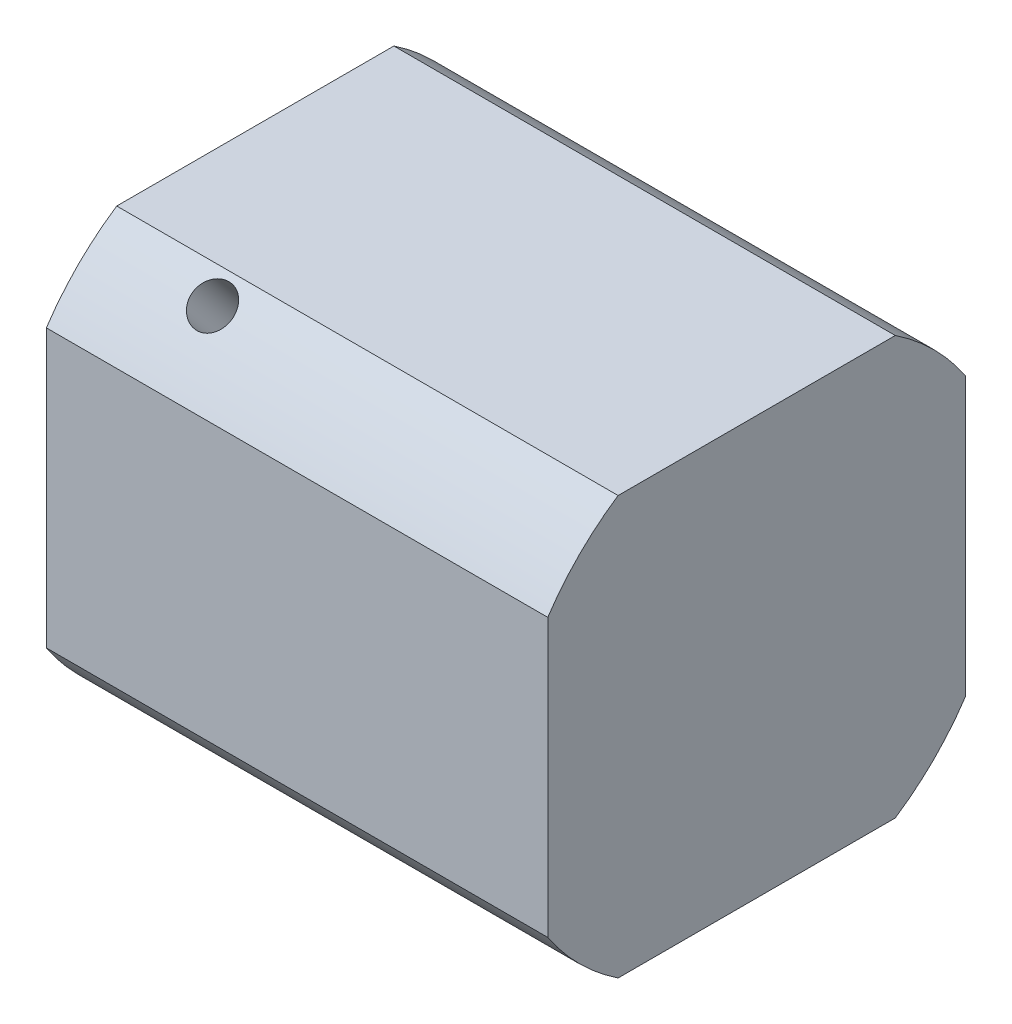
SolidWorks part; units mm, degrees
ref_plane "Front Plane" through (0, 0, 0) normal (0, 0, 1) x (1, 0, 0)
ref_plane "Top Plane" through (0, 0, 0) normal (0, 1, 0) x (1, 0, 0)
ref_plane "Right Plane" through (0, 0, 0) normal (1, 0, 0) x (0, 0, -1)
sketch "Sketch1" plane through (0, 0, 0) normal (0, 1, 0) x (1, 0, 0)
  line L0 (0, 0) -> (0, 19.05)
  line L1 (0, 19.05) -> (38.1, 19.05)
  line L2 (38.1, 19.05) -> (38.1, 9.525)
  line L5 (0, 0) -> (38.1, 0)
  line L6 (38.1, 9.525) -> (38.1, 0)
  dimension "D1" = 19.05
  dimension "D2" = 38.1
  dimension "D4" = 9.525
revolve "Revolve1" add sketch "Sketch1" angle 360 about L5
hole_wizard "Tap Drill for M3 Helicoil1" positions "3DSketch4" profile "Sketch8" hole size "M3x0.5" standard "ANSI Metric" end condition through all
sketch3d "3DSketch4"
  point P0 (8.9414, 14.6267, 12.205)
sketch "Sketch8" plane through (8.9414, 14.6267, 12.205) normal (1, 0, 0) x (0, -0.6407, 0.7678)
  line L0 (0, 0) -> (0, 45.8817)
  line L1 (0, 45.8817) -> (1.575, 45.8817)
  line L2 (1.575, 45.8817) -> (1.575, 0)
  line L5 (1.575, 0) -> (0, 0)
  line L11 (0, -6.35) -> (0, 107.95) construction
  dimension "Thru Hole Dia." = 3.15
  dimension "Thru Hole Depth" = 45.8817
sketch "Sketch10" plane through (0, 0, 0) normal (-1, 0, 0) x (0, 0, 1)
  line L0 (22.225, 22.225) -> (22.225, -22.225)
  line L1 (15.875, 15.875) -> (-15.875, 15.875)
  line L2 (15.875, 15.875) -> (15.875, -15.875)
  line L3 (15.875, -15.875) -> (-15.875, -15.875)
  line L4 (-15.875, 15.875) -> (-15.875, -15.875)
  line L5 (22.225, -22.225) -> (-22.225, -22.225)
  line L6 (-22.225, 22.225) -> (-22.225, -22.225)
  line L7 (22.225, 22.225) -> (-22.225, 22.225)
  dimension "D1" = 31.75
  dimension "D2" = 31.75
  dimension "D3" = 15.875
  dimension "D4" = 15.875
  dimension "D5" = 6.35
extrude "Cut-Extrude2" cut sketch "Sketch10" against normal through all
sketch "Sketch11" plane through (0, 0, 0) normal (-1, 0, 0) x (0, 0, 1)
  circle A0 centre (0, 0) radius 9.525
  dimension "D1" = 19.05
extrude "Cut-Extrude3" cut sketch "Sketch11" against normal blind 25.4
